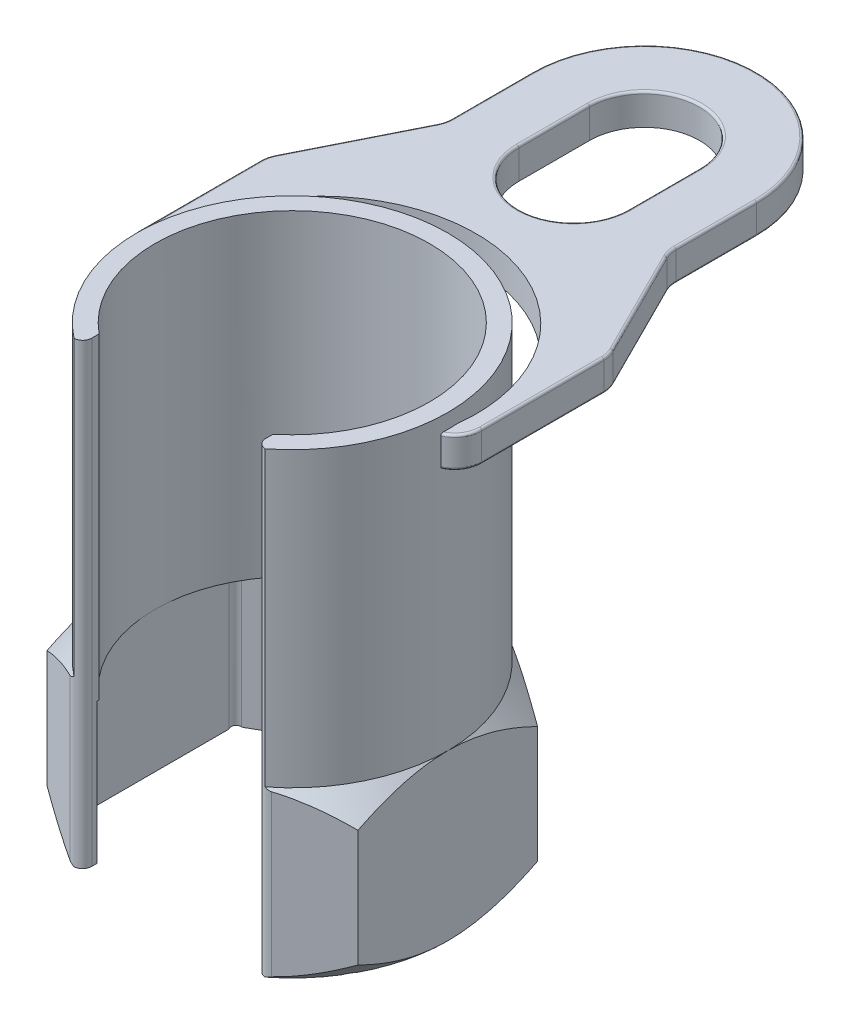
SolidWorks part; units mm, degrees
ref_plane "Front" through (0, 0, 0) normal (0, 0, 1) x (1, 0, 0)
ref_plane "Top" through (0, 0, 0) normal (0, 1, 0) x (1, 0, 0)
ref_plane "Right" through (0, 0, 0) normal (1, 0, 0) x (0, 0, -1)
sketch "Sketch1" plane through (0, 0, 0) normal (0, 1, 0) x (1, 0, 0)
  line L0 (-19, -23.2164) -> (-19, -28.2803)
  line L1 (0, 39.25) -> (-33.9915, 19.625)
  line L2 (0, 11.9615) -> (0, -7.933) construction
  line L3 (-33.9915, 19.625) -> (-33.9915, -19.625)
  line L4 (-33.9915, -19.625) -> (-19, -28.2803)
  line L5 (19, -28.2803) -> (33.9915, -19.625)
  line L6 (33.9915, -19.625) -> (33.9915, 19.625)
  line L7 (33.9915, 19.625) -> (0, 39.25)
  line L8 (19, -23.2164) -> (19, -28.2803)
  arc A0 (19, -28.1855) -> (-19, -28.1855) centre (0, 0) ccw construction
  arc A1 (19, -23.2164) -> (-19, -23.2164) centre (0, 0) ccw
  point P18 (-33.9915, -19.625)
  point P26 (33.9915, 19.625)
  dimension "D" = 78.5
  dimension "D2" = 60
  dimension "C" = 38
extrude "Extrude1" add sketch "Sketch1" along normal blind 36
sketch "Sketch3" plane through (0, 36, 0) normal (0, 1, 0) x (-1, 0, 0)
  line L0 (-33.9915, 19.625) -> (-33.9915, -19.625) construction
  line L2 (-19, 28.1854) -> (-19, 23.2164)
  line L3 (19, 28.1854) -> (19, 23.2164)
  arc A0 (-19, 23.2164) -> (19, 23.2164) centre (0, 0) ccw
  arc A1 (-19, 23.2164) -> (19, 23.2164) centre (0, 0) ccw construction
  arc A2 (-19, 28.1854) -> (19, 28.1854) centre (0, 0) ccw
  dimension "D1" = 0.0001
extrude "Extrude2" add sketch "Sketch3" along normal blind 64
sketch "Sketch8" plane through (0, 0, 0) normal (0, -1, 0) x (1, 0, 0)
  line L1 (33.9915, 19.625) -> (33.9915, -19.625) construction
  circle A0 centre (0, 0) radius 33.9915
extrude "Cut-Extrude4" cut sketch "Sketch8" against normal through all draft 45 flip side to cut
sketch "Sketch19" plane through (0, 36, 0) normal (0, 1, 0) x (-1, 0, 0)
  circle A1 centre (0, 0) radius 33.9914
  arc A2 (-19, 28.1854) -> (19, 28.1854) centre (0, 0) ccw construction
extrude "Cut-Extrude6" cut sketch "Sketch19" against normal through all draft 45 flip side to cut
sketch "Sketch26" plane through (0, 0, 0) normal (0, -1, 0) x (1, 0, 0)
  line L1 (-30, -17.3205) -> (0, -34.641)
  line L2 (0, -34.641) -> (30, -17.3205)
  line L3 (30, -17.3205) -> (30, 17.3205)
  line L4 (30, 17.3205) -> (0, 34.641)
  line L5 (0, 34.641) -> (-30, 17.3205)
  line L6 (-30, 17.3205) -> (-30, -17.3205)
  circle A0 centre (0, 0) radius 30 construction
  dimension "D1" = 60
extrude "Cut-Extrude9" cut sketch "Sketch26" against normal up to vertex (38.5 mm away)
fillet "Fillet1" radius 2 7 edges at (-30, 15.6955, -17.3205) (-30, 15.6955, 17.3205) (30, 15.6955, 17.3205) (30, 15.6955, -17.3205) (-19, 17.9999, 28.2803) (19, 17.9999, 28.2803) (0, 15.6955, -34.641)
sketch "Sketch4" [suppressed] plane through (0, 0, 0) normal (0, 1, 0) x (-1, 0, 0)
  line L0 (0, -11.2014) -> (0, 12.8888) construction
  line L1 (-10, -2.5) -> (10, -2.5)
  line L2 (-10, -2.5) -> (-10, 3.8)
  line L3 (-10, 3.8) -> (10, 3.8)
  line L4 (10, -2.5) -> (10, 3.8)
  line L5 (16.2585, 0) -> (-21.4153, 0) construction
  dimension "D1" = 60
  dimension "D2" = 11
  dimension "D3" = 9.7
sketch "Sketch12" [suppressed] plane through (0, 0, 0) normal (0, 1, 0) x (1, 0, 0)
  line L0 (-11, -4) -> (11, -4)
  line L1 (0, 0) -> (-11.4274, 0) construction
  line L2 (-11, 2.7) -> (11, 2.7)
  line L3 (-4.5, 14.3091) -> (4.5, 14.3091)
  line L4 (-7, 3.2909) -> (-7, -3.2909) construction
  line L5 (7, -3.2909) -> (7, 3.2909) construction
  arc A0 (-11, -4) -> (11, -4) centre (0, 0) ccw
  arc A1 (-6.3246, -3) -> (6.3246, -3) centre (0, 0) ccw construction
  arc A2 (-4.5, 14.3091) -> (-11, 2.7) centre (2.617, 2.7) ccw
  arc A3 (-4.5, 14.3091) -> (4.5, 14.3091) centre (0, 0) ccw construction
  arc A4 (4.5, 14.3091) -> (11, 2.7) centre (-2.617, 2.7) cw
ref_plane "Plane3" through (0, 90, 0) normal (0, 1, 0) x (-1, 0, 0)
sketch "Sketch16" plane through (0, 90, 0) normal (0, 1, 0) x (-1, 0, 0)
  line L5 (0, 0) -> (0, 54.2988) construction
  line L6 (-24.5, -77) -> (-24.5, -59.3928)
  line L10 (24.5, -59.3928) -> (24.5, -77)
  line L11 (36.8771, -33.2458) -> (25.1229, -56.7542)
  line L12 (-36.8771, -33.2458) -> (-25.1229, -56.7542)
  line L13 (-37.5, -3.9082) -> (-37.5, -30.6072)
  line L14 (37.5, -3.9082) -> (37.5, -30.6072)
  line L15 (38.3763, 1.5) -> (-38.1367, 1.5) construction
  arc A0 (-20.8917, 26.8133) -> (20.8917, 26.8133) centre (0, 0) ccw construction
  arc A1 (-33.9583, 1.5) -> (33.9583, 1.5) centre (0, 0) ccw
  arc A2 (37.5, -3.9082) -> (33.9583, 1.5) centre (31.6, -3.9082) ccw
  arc A3 (-37.5, -3.9082) -> (-33.9583, 1.5) centre (-31.6, -3.9082) cw
  arc A4 (-37.5, -30.6072) -> (-36.8771, -33.2458) centre (-31.6, -30.6072) ccw
  arc A5 (-25.1229, -56.7542) -> (-24.5, -59.3928) centre (-30.4, -59.3928) cw
  arc A7 (37.5, -30.6072) -> (36.8771, -33.2458) centre (31.6, -30.6072) cw
  arc A8 (25.1229, -56.7542) -> (24.5, -59.3928) centre (30.4, -59.3928) ccw
  arc A15 (24.5, -77) -> (-24.5, -77) centre (0, -77) cw
  point P18 (-37.5, -32)
  point P22 (-24.5, -58)
  point P25 (37.5, -32)
  point P30 (24.5, -58)
  dimension "D1" = 75
  dimension "D2" = 32
  dimension "D3" = 58
  dimension "D4" = 5.9
  dimension "D6" = 49
  dimension "D7" = 77
  dimension "D14" = 1.5
extrude "Extrude7" add sketch "Sketch16" along normal blind 6.8
sketch "Sketch25" plane through (0, 96.8, 0) normal (0, -1, 0) x (1, 0, 0)
  line L1 (-29.4486, 0) -> (37.9585, 0) construction
  line L3 (0, -57.3769) -> (0, 10.8445) construction
  line L4 (-12, -77) -> (-12, -61.5)
  line L5 (12, -77) -> (12, -61.5)
  arc A0 (-20.8917, 26.8133) -> (20.8917, 26.8133) centre (0, 0) ccw construction
  arc A2 (-24.5, -77) -> (24.5, -77) centre (0, -77) ccw construction
  arc A6 (33.9325, -2) -> (-33.9325, -2) centre (0, 0) cw
  arc A7 (33.9325, -2) -> (-33.9325, -2) centre (0, -6) cw
  arc A8 (12, -77) -> (-12, -77) centre (0, -77) cw
  arc A9 (12, -61.5) -> (-12, -61.5) centre (0, -61.5) ccw
  dimension "D1" = 40
  dimension "D2" = 24
  dimension "D3" = 2
  dimension "D4" = 6
extrude "Cut-Extrude8" cut sketch "Sketch25" along normal up to next
fillet "Fillet4" radius 0.5 30 edges at (12, 96.8, -69.25) (0, 96.8, -89) (-12, 96.8, -69.25) (36.5358, 96.8, -0.6758) (37.5, 96.8, -17.2577) (37.3422, 96.8, -31.9627) (-36.5358, 96.8, -0.6758) (-37.5, 96.8, -17.2577) (-37.3422, 96.8, -31.9627) (-31, 96.8, -45) (-24.6578, 96.8, -58.0373) (-24.5, 96.8, -68.1964) (0, 96.8, -101.5) (24.5, 96.8, -68.1964) (24.6578, 96.8, -58.0373) (36.5358, 90, -0.6758) (37.5, 90, -17.2577) (37.3422, 90, -31.9627) (-36.5358, 90, -0.6758) (-37.5, 90, -17.2577) (-37.3422, 90, -31.9627) (-31, 90, -45) (-24.6578, 90, -58.0373) (-24.5, 90, -68.1964) (0, 90, -101.5) (24.5, 90, -68.1964) (24.6578, 90, -58.0373) (0, 96.8, -49.5) (31, 96.8, -45) (31, 90, -45)
sketch "Sketch20" [suppressed] plane through (0, 0, 0) normal (0, 1, 0) x (1, 0, 0)
  line L0 (0, 0) -> (0, 12.8849) construction
  line L1 (-7.5, -9.3675) -> (-7.5, -14.4157)
  line L2 (7.5, -9.3675) -> (7.5, -14.4157)
  arc A0 (7.5, -14.4157) -> (-7.5, -14.4157) centre (0, 0) ccw
  arc A1 (7.5, -9.3675) -> (-7.5, -9.3675) centre (0, 0) ccw
  circle A2 centre (0, 0) radius 16.25 construction
  circle A3 centre (0, 0) radius 12 construction
  dimension "D1" = 78.5
  dimension "D2" = 60
  dimension "D3" = 38
extrude "Extrude3" [suppressed] add sketch "Sketch20" along normal blind 68
ref_plane "Plane7" [suppressed] through (0, 41.999, 0) normal (0, 1, 0) x (-1, 0, 0)
sketch "Sketch21" [suppressed] plane through (0, 41.999, 0) normal (0, 1, 0) x (-1, 0, 0)
  line L1 (2.5, 16.0565) -> (2.5, 19.8734)
  line L2 (7.5, 14.4157) -> (7.5, 9.3675) construction
  line L4 (7.5, 14.4157) -> (7.5, 18.5729)
  arc A1 (2.5, 16.0565) -> (7.5, 14.4157) centre (0, 0) ccw
  arc A2 (2.5, 19.8734) -> (7.5, 18.5729) centre (0, 0) ccw
  arc A3 (-7.5, 14.4157) -> (7.5, 14.4157) centre (0, 0) ccw construction
  dimension "D1" = 6.12
  dimension "D2" = 2.5
extrude "Extrude4" [suppressed] add sketch "Sketch21" against normal blind 19.5 separate body
ref_plane "Plane6" [suppressed] through (5.0421, 41.999, -19.385) normal (0.2517, 0, -0.9678) x (-0.9678, 0, -0.2517)
sketch "Sketch22" [suppressed] plane through (5.0421, 41.999, -19.385) normal (0.2517, 0, -0.9678) x (-0.9678, 0, -0.2517)
  line L0 (20.03, 0) -> (-20.03, 0) construction
  line L1 (0, 0) -> (0, 14.8678) construction
  line L2 (-3.2, -3.3) -> (3.2, -3.3)
  line L3 (-3.2, -3.3) -> (-3.2, -9.7)
  line L4 (-3.2, -9.7) -> (3.2, -9.7)
  line L5 (3.2, -3.3) -> (3.2, -9.7)
  line L7 (-18.9345, -6.5) -> (19.4735, -6.5) construction
  dimension "D1" = 11.6
  dimension "D2" = 9.75
  dimension "D3" = 11.6
extrude "Extrude5" [suppressed] add sketch "Sketch22" along normal blind 25 and the other way up to next
sketch "Sketch23" [suppressed] plane through (8.0628, 0, -30.9986) normal (0.2517, 0, -0.9678) x (-0.9678, 0, -0.2517)
  circle A0 centre (0, 35.499) radius 4.5255
extrude "Extrude6" [suppressed] add sketch "Sketch23" along normal blind 58 draft 2
dome "Dome1" [suppressed] faces to dome 1 distance 3 parameters "D1"=3
sketch "Sketch24" [suppressed] plane through (0, 0, 0) normal (0, -1, 0) x (1, 0, 0)
  line L2 (-12, 6.9282) -> (-12, -6.9282)
  line L3 (-12, -6.9282) -> (0, -13.8564)
  line L4 (0, -13.8564) -> (12, -6.9282)
  line L5 (12, -6.9282) -> (12, 6.9282)
  line L6 (12, 6.9282) -> (0, 13.8564)
  line L7 (0, 13.8564) -> (-12, 6.9282)
  circle A0 centre (0, 0) radius 12 construction
  dimension "D1" = 60
extrude "Cut-Extrude7" [suppressed] cut sketch "Sketch24" against normal through all
fillet "Fillet2" [suppressed] radius 0.5
fillet "Fillet3" [suppressed] radius 0.5
fillet "Fillet5" [suppressed] radius 1
